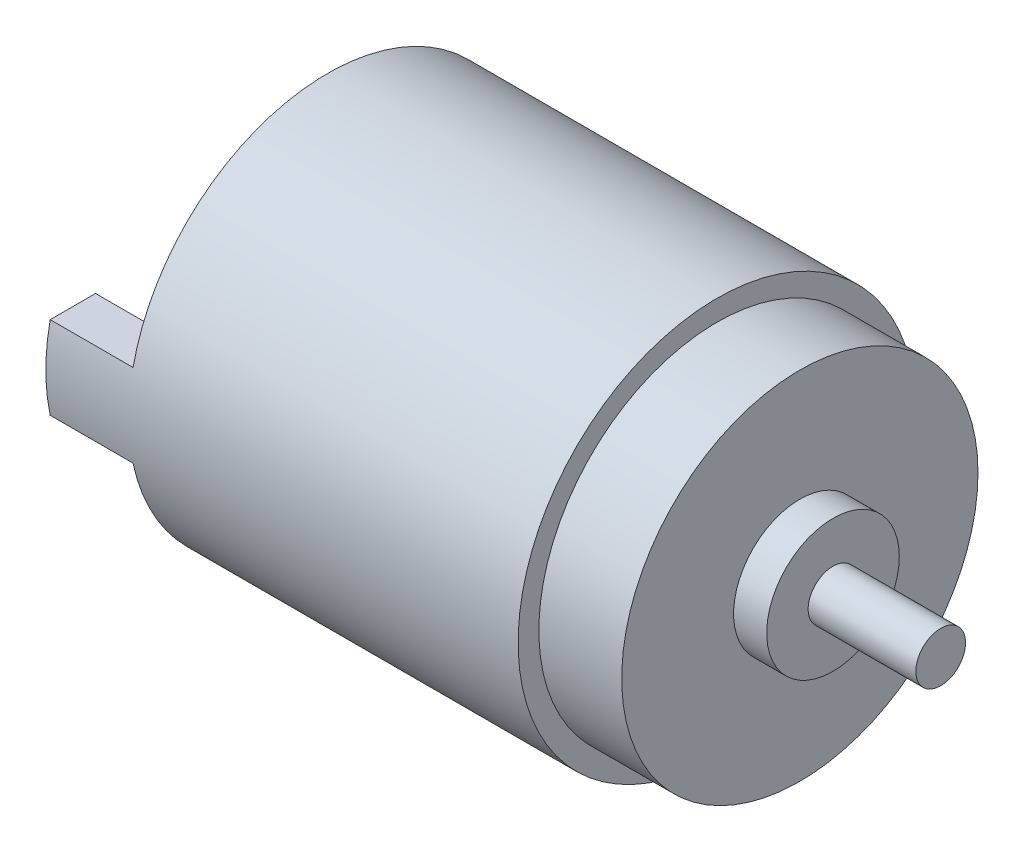
SolidWorks part; units mm, degrees
ref_plane "前视基准面" through (0, 0, 0) normal (0, 0, 1) x (1, 0, 0)
ref_plane "上视基准面" through (0, 0, 0) normal (0, 1, 0) x (1, 0, 0)
ref_plane "右视基准面" through (0, 0, 0) normal (1, 0, 0) x (0, 0, -1)
sketch "草图1" plane through (0, 0, 0) normal (1, 0, 0) x (0, 0, -1)
  circle A0 centre (0, 0) radius 12
  dimension "D1" = 24
extrude "凸台-拉伸1" add sketch "草图1" along normal blind 23.5
sketch "草图2" plane through (23.5, 0, 0) normal (1, 0, 0) x (0, 0, -1)
  circle A0 centre (0, 0) radius 1.5
extrude "凸台-拉伸2" add sketch "草图2" along normal blind 13.5
sketch "草图3" plane through (23.5, 0, 0) normal (1, 0, 0) x (0, 0, -1)
  circle A0 centre (0, 0) radius 10.75
  dimension "D1" = 21.5
extrude "凸台-拉伸3" add sketch "草图3" along normal blind 5
sketch "草图4" plane through (28.5, 0, 0) normal (1, 0, 0) x (0, 0, -1)
  circle A0 centre (0, 0) radius 4
  dimension "D1" = 8
extrude "凸台-拉伸4" add sketch "草图4" along normal blind 2
sketch "草图5" plane through (0, 0, 0) normal (-1, 0, 0) x (0, 0, 1)
  line L0 (-2.0616, -4) -> (2.0616, -4)
  arc A0 (2.0616, -4) -> (-2.0616, -4) centre (0, 0) ccw
  dimension "D1" = 9
  dimension "D2" = 4
extrude "凸台-拉伸5" add sketch "草图5" along normal blind 2
sketch "草图6" plane through (0, 0, 0) normal (-1, 0, 0) x (0, 0, 1)
  line L0 (0, 0) -> (14.3141, 0) construction
  line L2 (9, 2.5) -> (11.7367, 2.5)
  line L3 (9, 2.5) -> (9, -2.5)
  line L4 (9, -2.5) -> (11.7367, -2.5)
  circle A0 centre (0, 0) radius 12
  circle A1 centre (0, 0) radius 12 construction
  point P10 (11.7367, 2.5)
  point P11 (11.7367, -2.5)
  circle M8 centre (0, 0) radius 12
  dimension "D1" = 3
  dimension "D2" = 5
extrude "凸台-拉伸6" add sketch "草图6" along normal blind 5 contours L3 L0 A0 L2 | L0 L3 L4 M8
mirror "镜向1" about plane through (0, 0, 0) normal (0, 0, 1) of "凸台-拉伸6"
